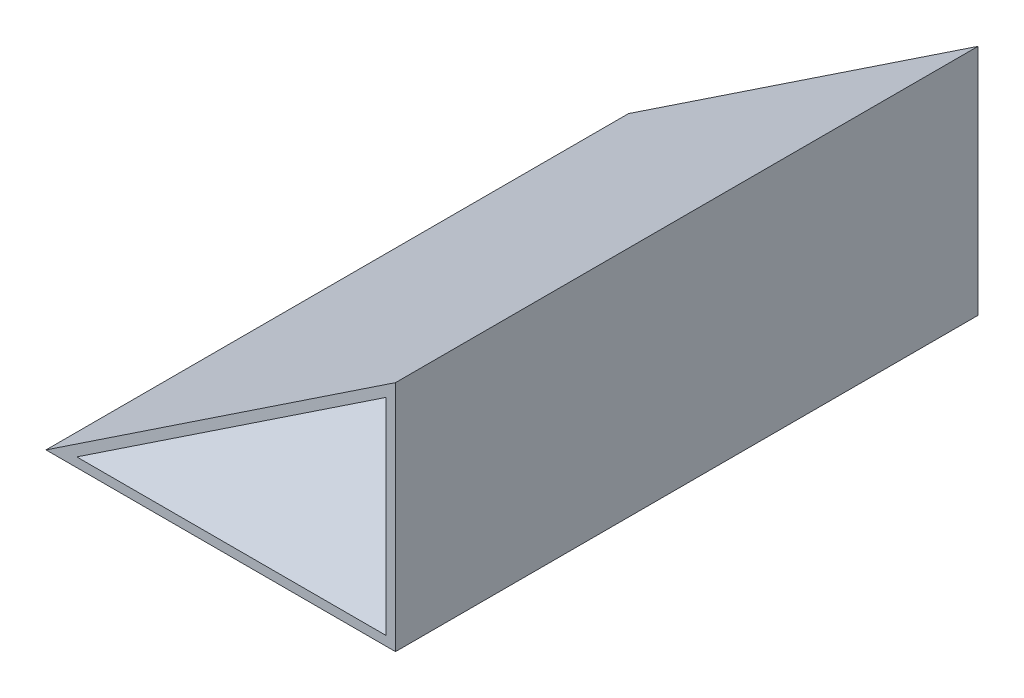
SolidWorks part; units mm, degrees
ref_plane "前视基准面" through (0, 0, 0) normal (0, 0, 1) x (1, 0, 0)
ref_plane "上视基准面" through (0, 0, 0) normal (0, 1, 0) x (1, 0, 0)
ref_plane "右视基准面" through (0, 0, 0) normal (1, 0, 0) x (0, 0, -1)
other "Configuration Table"
sketch "草图1" plane through (0, 0, 0) normal (0, 0, 1) x (1, 0, 0)
  line L0 (-104.6414, -31.8565) -> (45.3586, -31.8565)
  line L1 (45.3586, -31.8565) -> (45.3586, 68.1435)
  line L2 (45.3586, 68.1435) -> (-104.6414, -31.8565)
  dimension "D1" = 100
  dimension "D2" = 150
extrude "凸台-拉伸1" add sketch "草图1" along normal blind 250
sketch "草图2" plane through (0, 0, 250) normal (0, 0, 1) x (1, 0, 0)
  line L0 (41.3586, 60.6694) -> (41.3586, -27.8565)
  line L1 (45.3586, -31.8565) -> (45.3586, 68.1435) construction
  line L2 (-91.4302, -27.8565) -> (41.3586, -27.8565)
  line L3 (-104.6414, -31.8565) -> (45.3586, -31.8565) construction
  line L4 (-91.4302, -27.8565) -> (41.3586, 60.6694)
  line L5 (45.3586, 68.1435) -> (-104.6414, -31.8565) construction
  dimension "D1" = 4
  dimension "D2" = 4
  dimension "D3" = 4
extrude "切除-拉伸1" cut sketch "草图2" against normal through all
